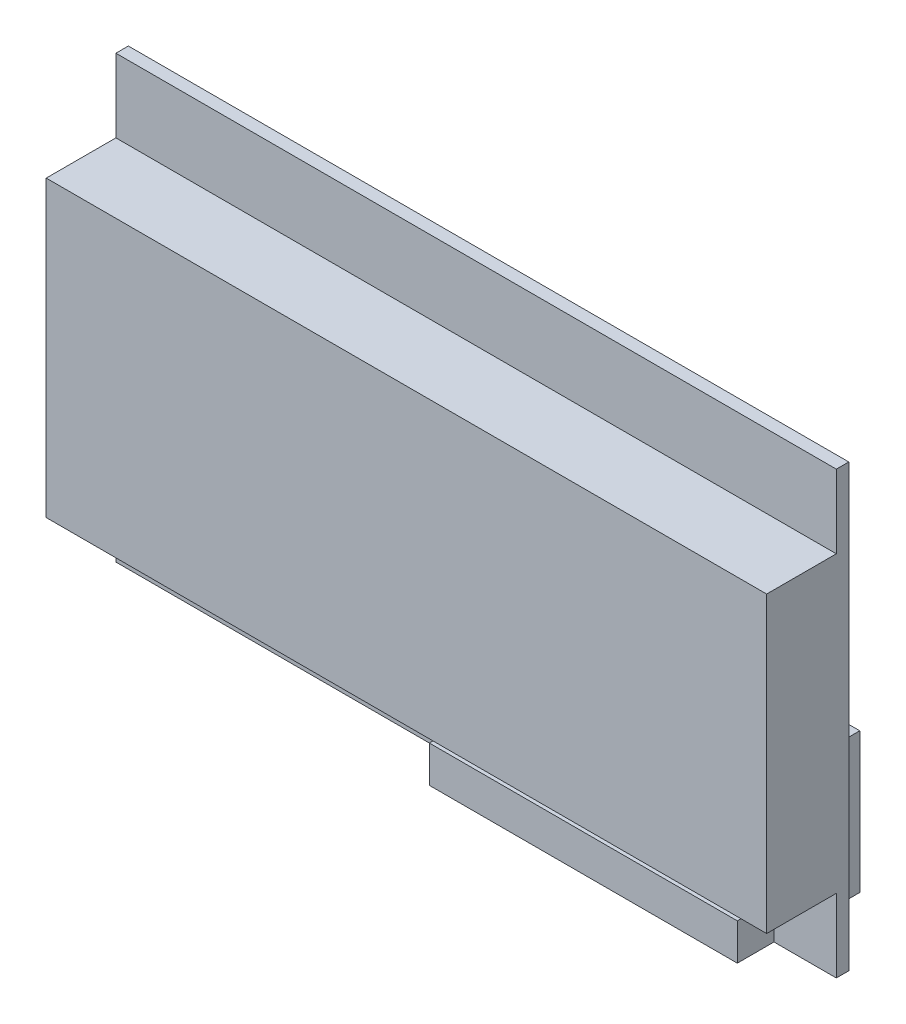
SolidWorks part; units mm, degrees
ref_plane "Спереди" through (0, 0, 0) normal (0, 0, 1) x (1, 0, 0)
ref_plane "Сверху" through (0, 0, 0) normal (0, 1, 0) x (1, 0, 0)
ref_plane "Справа" through (0, 0, 0) normal (1, 0, 0) x (0, 0, -1)
other "Configuration Table"
sketch "Эскиз1" plane through (0, 0, 0) normal (0, 0, 1) x (1, 0, 0)
  line L1 (0, 0) -> (98.25, 0)
  line L2 (0, 0) -> (0, 60.1)
  line L3 (0, 60.1) -> (98.25, 60.1)
  line L4 (98.25, 0) -> (98.25, 60.1)
  dimension "D1" = 60.1
  dimension "D2" = 98.25
extrude "Бобышка-Вытянуть1" add sketch "Эскиз1" along normal blind 1.7
sketch "Эскиз2" plane through (0, 0, 1.7) normal (0, 0, 1) x (1, 0, 0)
  line L0 (0, 60.1) -> (0, 0) construction
  line L1 (0, 50.1) -> (98.25, 50.1)
  line L2 (0, 50.1) -> (0, 10)
  line L3 (0, 10) -> (98.25, 10)
  line L4 (98.25, 50.1) -> (98.25, 10)
  line L5 (98.25, 0) -> (98.25, 60.1) construction
  line L6 (98.25, 60.1) -> (0, 60.1) construction
  line L7 (0, 0) -> (98.25, 0) construction
  dimension "D1" = 10
  dimension "D2" = 10
extrude "Бобышка-Вытянуть2" add sketch "Эскиз2" along normal blind 9.5
sketch "Эскиз3" plane through (0, 0, 1.7) normal (0, 0, 1) x (1, 0, 0)
  line L0 (0, 0) -> (98.25, 0) construction
  line L1 (89.75, 0) -> (47.75, 0)
  line L2 (89.75, 0) -> (89.75, 5)
  line L3 (89.75, 5) -> (47.75, 5)
  line L4 (47.75, 0) -> (47.75, 5)
  line L5 (98.25, 0) -> (98.25, 10) construction
  dimension "D1" = 42
  dimension "D2" = 5
  dimension "D3" = 8.5
extrude "Бобышка-Вытянуть3" add sketch "Эскиз3" along normal blind 5
sketch "Эскиз4" plane through (0, 0, 0) normal (0, 0, -1) x (-1, 0, 0)
  line L0 (0, 0) -> (-98.25, 0) construction
  line L1 (-89.75, 0) -> (-47.75, 0)
  line L2 (-89.75, 0) -> (-89.75, 19.1)
  line L3 (-89.75, 19.1) -> (-47.75, 19.1)
  line L4 (-47.75, 0) -> (-47.75, 19.1)
  line L5 (-47.75, 5) -> (-47.75, 0) construction
  line L6 (-89.75, 0) -> (-89.75, 5) construction
  dimension "D1" = 0
  dimension "D2" = 0
  dimension "D3" = 19.1
extrude "Бобышка-Вытянуть4" add sketch "Эскиз4" along normal blind 10
